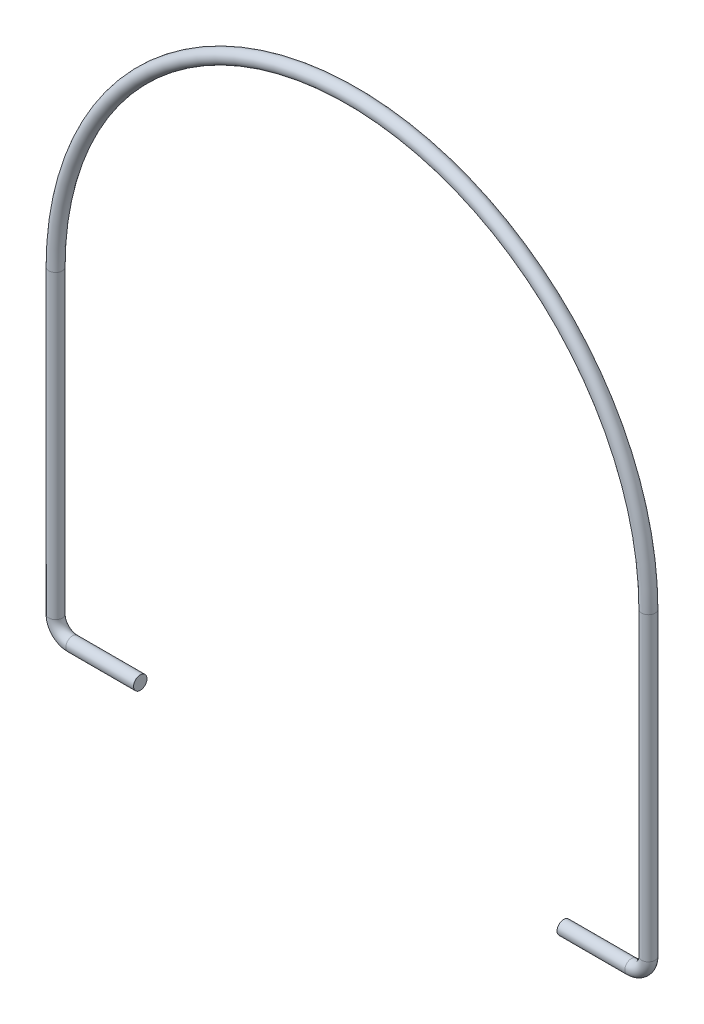
SolidWorks part; units mm, degrees
ref_plane "Front Plane" through (0, 0, 0) normal (0, 0, 1) x (1, 0, 0)
ref_plane "Top Plane" through (0, 0, 0) normal (0, 1, 0) x (1, 0, 0)
ref_plane "Right Plane" through (0, 0, 0) normal (1, 0, 0) x (0, 0, -1)
sketch "Sketch1" plane through (0, 0, 0) normal (0, 0, 1) x (1, 0, 0)
  line L0 (0, 0) -> (-16, 0)
  line L1 (-20, 4) -> (-20, 75)
  line L3 (120, 75) -> (120, 4)
  line L4 (116, 0) -> (100, 0)
  arc A0 (120, 75) -> (-20, 75) centre (50, 75) ccw
  arc A1 (120, 4) -> (116, 0) centre (116, 4) cw
  arc A2 (-20, 4) -> (-16, 0) centre (-16, 4) ccw
  point P10 (120, 0)
  point P13 (-20, 0)
  dimension "D1" = 75
  dimension "D4" = 70
  dimension "D5" = 4
  dimension "D2" = 20
  dimension "D3" = 20
sketch "Sketch2" plane through (0, 0, 0) normal (1, 0, 0) x (0, 0, -1)
  circle A0 centre (0, 0) radius 1.5875
  dimension "D1" = 3.175
sweep "Sweep1" add profiles "Sketch2" path "Sketch1"
